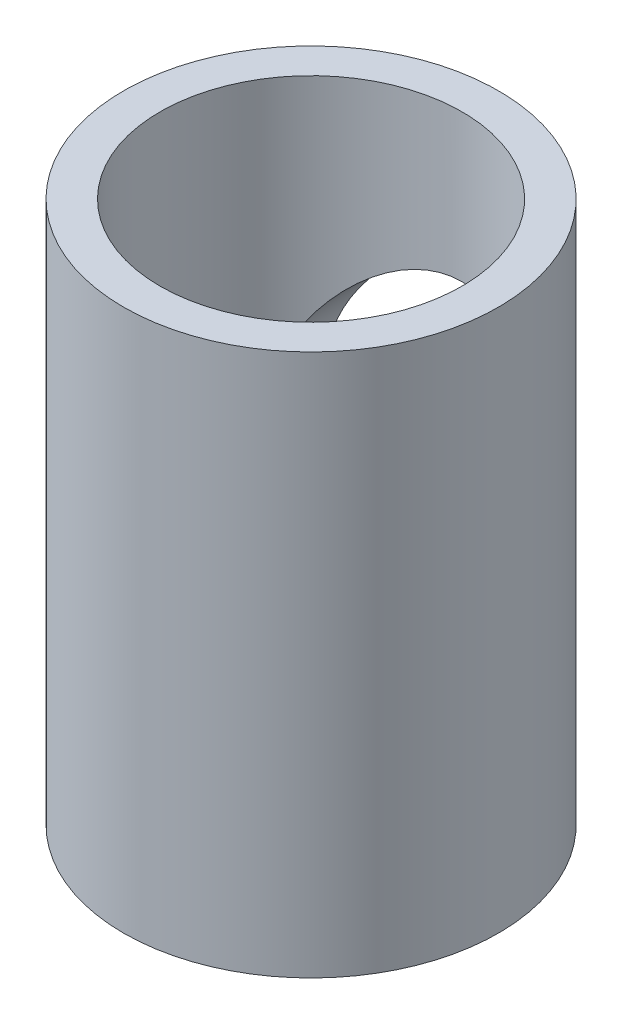
SolidWorks part; units mm, degrees
ref_plane "Front Plane" through (0, 0, 0) normal (0, 0, 1) x (1, 0, 0)
ref_plane "Top Plane" through (0, 0, 0) normal (0, 1, 0) x (1, 0, 0)
ref_plane "Right Plane" through (0, 0, 0) normal (1, 0, 0) x (0, 0, -1)
sketch "Sketch1" plane through (0, 0, 0) normal (0, 1, 0) x (1, 0, 0)
  circle A0 centre (0, 0) radius 2.4765
  circle A1 centre (0, 0) radius 3.0734
  dimension "D1" = 4.953
  dimension "D2" = 6.1468
extrude "Boss-Extrude1" add sketch "Sketch1" along normal blind 8.89
sketch "Sketch2" plane through (0, 0, 0) normal (0, 0, 1) x (1, 0, 0)
  line L0 (0, 4.445) -> (0, 0) construction
  circle A0 centre (0, 4.445) radius 2.032
  dimension "D1" = 4.064
  dimension "D2" = 4.445
extrude "Cut-Extrude1" cut sketch "Sketch2" against normal blind 8.89
